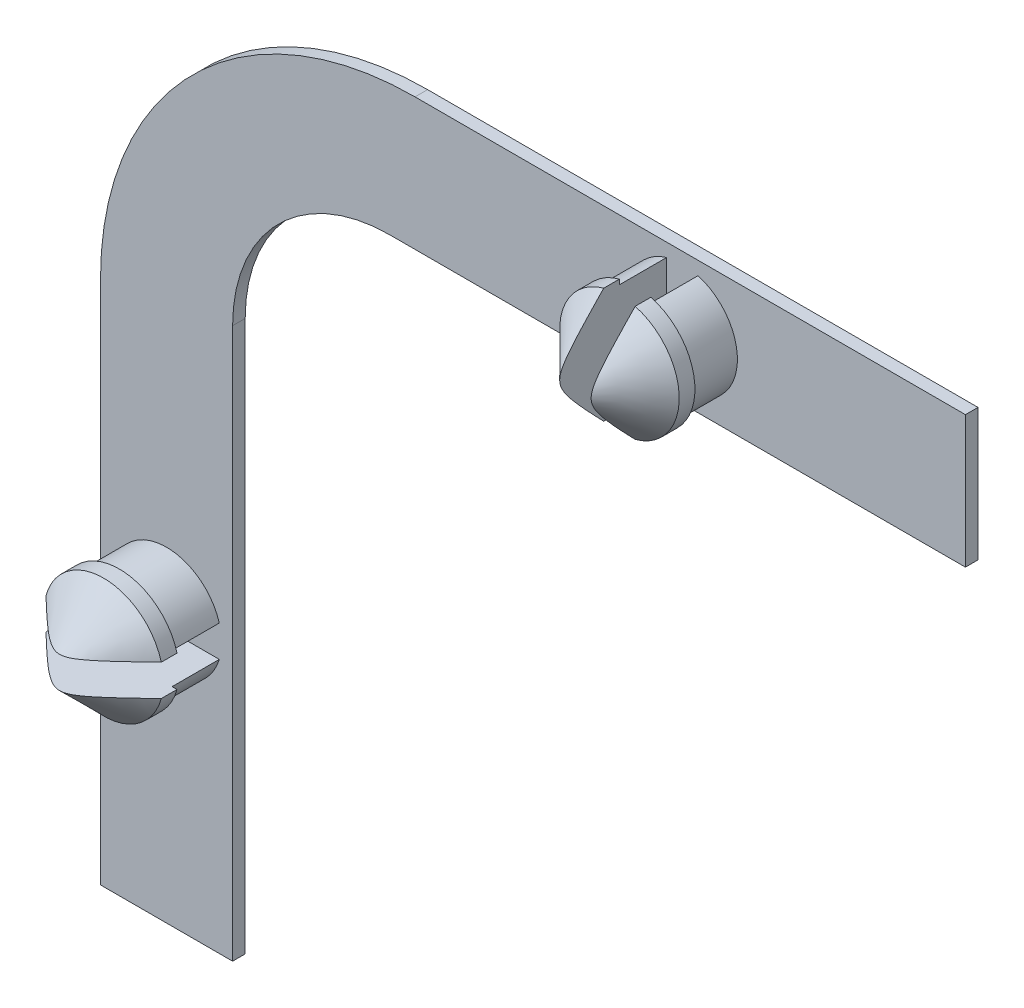
SolidWorks part; units mm, degrees
ref_plane "Přední rovina" through (0, 0, 0) normal (0, 0, 1) x (1, 0, 0)
ref_plane "Horní rovina" through (0, 0, 0) normal (0, 1, 0) x (1, 0, 0)
ref_plane "Pravá rovina" through (0, 0, 0) normal (1, 0, 0) x (0, 0, -1)
sketch "Skica2" plane through (0, 0, 0) normal (0, 0, 1) x (1, 0, 0)
  line L1 (-13.75, 2.1) -> (13.75, 2.1)
  line L2 (-13.75, 2.1) -> (-13.75, -2.1)
  line L3 (-13.75, -2.1) -> (13.75, -2.1)
  line L4 (13.75, 2.1) -> (13.75, -2.1)
  line L5 (-13.75, 2.1) -> (13.75, -2.1) construction
  line L6 (-13.75, -2.1) -> (13.75, 2.1) construction
  point P0 (0, 0)
  point P5 (-1, -0.2)
  dimension "D1" = 4.2
  dimension "D2" = 27.5
extrude "Přidat vysunutím2" add sketch "Skica2" along normal blind 0.4
sketch "Skica3" plane through (0, 0, 0.4) normal (0, 0, 1) x (1, 0, 0)
  line L1 (13.75, -2.1) -> (13.75, 2.1) construction
  circle A1 centre (4.75, 0) radius 1.75
  dimension "D3" = 3.5
  dimension "D4" = 9
extrude "Přidat vysunutím3" add sketch "Skica3" along normal blind 1.5
sketch "Skica5" plane through (0, 0, 1.9) normal (0, 0, 1) x (1, 0, 0)
  circle A1 centre (4.75, 0) radius 1.9
  dimension "D2" = 3.8
extrude "Přidat vysunutím5" add sketch "Skica5" along normal blind 2
chamfer "Zkosení2" distance 1.5 angle 45 1 edges at (6.65, 0, 3.9)
sketch "Skica7" plane through (0, 0, 3.9) normal (0, 0, 1) x (1, 0, 0)
  line L7 (4.25, 2.5) -> (5.25, 2.5)
  line L8 (4.25, 2.5) -> (4.25, -2.5)
  line L9 (4.25, -2.5) -> (5.25, -2.5)
  line L10 (5.25, 2.5) -> (5.25, -2.5)
  line L11 (4.25, 2.5) -> (5.25, -2.5) construction
  line L12 (4.25, -2.5) -> (5.25, 2.5) construction
  point P1 (0, 0)
  point P5 (4.75, 0)
  dimension "D3" = 5
  dimension "D4" = 1
extrude "Odebrat vysunutím1" cut sketch "Skica7" against normal blind 3.5
sketch "Skica8" plane through (0, 0, 0) normal (0, 0, -1) x (-1, 0, 0)
  line L8 (13.75, -2.1) -> (9.55, -2.1)
  line L9 (13.75, -2.1) -> (13.75, -24.6)
  line L10 (13.75, -24.6) -> (9.55, -24.6)
  line L11 (9.55, -2.1) -> (9.55, -24.6)
  dimension "D1" = 22.5
  dimension "D2" = 4.2
extrude "Přidat vysunutím6" add sketch "Skica8" against normal blind 0.4
sketch "Skica9" plane through (0, 0, 0.4) normal (0, 0, 1) x (1, 0, 0)
  line L2 (-13.75, 2.1) -> (-13.75, -24.6) construction
  circle A0 centre (-11.65, -16) radius 1.75
  dimension "D1" = 3.5
  dimension "D2" = 2.1
extrude "Přidat vysunutím7" add sketch "Skica9" along normal blind 1.5
sketch "Skica10" plane through (0, 0, 1.9) normal (0, 0, 1) x (1, 0, 0)
  circle A0 centre (-11.65, -16) radius 1.9
  circle A1 centre (-11.65, -16) radius 1.75 construction
  dimension "D1" = 3.8
  dimension "D3" = 0
extrude "Přidat vysunutím8" add sketch "Skica10" along normal blind 2
chamfer "Zkosení3" distance 1.5 angle 45 1 edges at (-9.75, -16, 3.9)
sketch "Skica12" plane through (0, 0, 3.9) normal (0, 0, 1) x (1, 0, 0)
  line L1 (-14.15, -15.5) -> (-9.15, -15.5)
  line L2 (-14.15, -15.5) -> (-14.15, -16.5)
  line L3 (-14.15, -16.5) -> (-9.15, -16.5)
  line L4 (-9.15, -15.5) -> (-9.15, -16.5)
  line L5 (-14.15, -15.5) -> (-9.15, -16.5) construction
  line L6 (-14.15, -16.5) -> (-9.15, -15.5) construction
  point P0 (-11.65, -16)
  dimension "D1" = 1
  dimension "D2" = 5
extrude "Odebrat vysunutím2" cut sketch "Skica12" against normal blind 3.5
fillet "Zaoblit1" radius 5 1 edges at (-9.55, -2.1, 0.2)
fillet "Zaoblit2" radius 10 1 edges at (-13.75, 2.1, 0.2)
equation "\"1.5.000mm\"=10"
